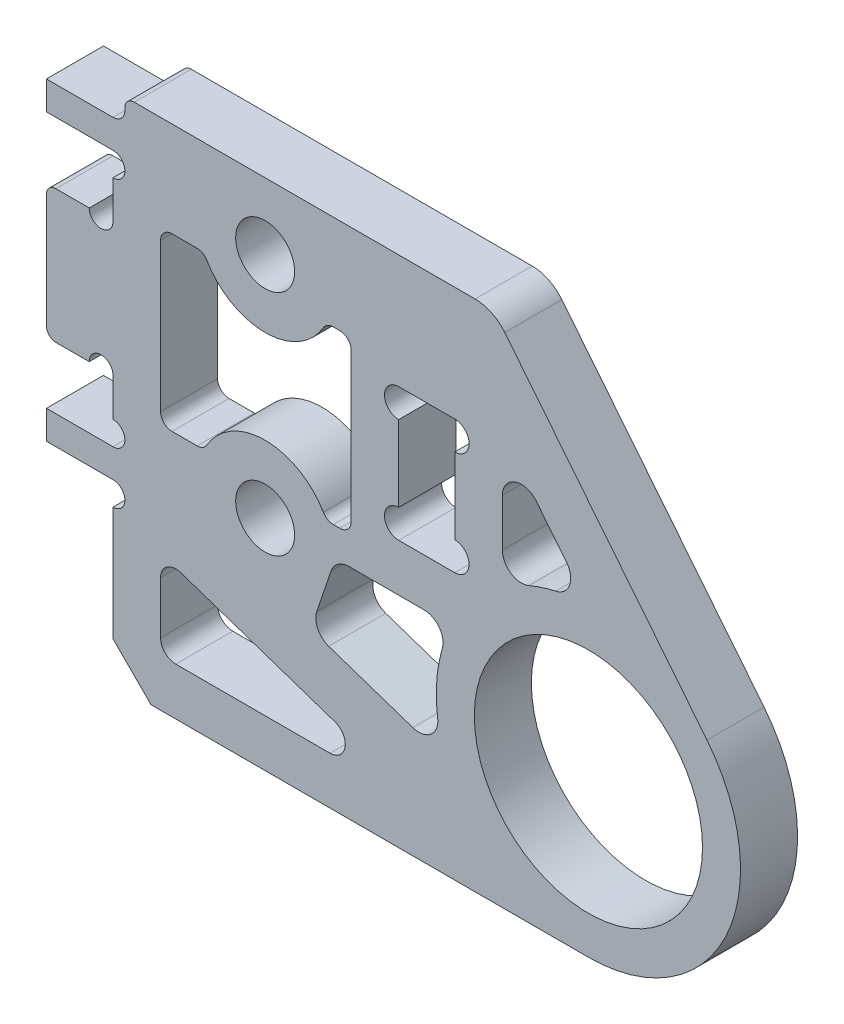
SolidWorks part; units mm, degrees
ref_plane "前视基准面" through (0, 0, 0) normal (0, 0, 1) x (1, 0, 0)
ref_plane "上视基准面" through (0, 0, 0) normal (0, 1, 0) x (1, 0, 0)
ref_plane "右视基准面" through (0, 0, 0) normal (1, 0, 0) x (0, 0, -1)
sketch "草图1" plane through (0, 0, 0) normal (0, 0, 1) x (1, 0, 0)
  line L0 (-5, 19) -> (6.2372, 5.0098)
  line L1 (-25, 19) -> (-25, 0)
  line L3 (-25, 19) -> (-5, 19)
  line L4 (-25, 0) -> (-2.56, -7.5793)
  arc A0 (-2.56, -7.5793) -> (6.2372, 5.0098) centre (0, 0) ccw
  circle A1 centre (0, 0) radius 6
  point P4 (-25, 9.5)
  dimension "D1" = 16
  dimension "D2" = 12
  dimension "D3" = 9.5
  dimension "D4" = 19
  dimension "D5" = 25
  dimension "D6" = 20
extrude "凸台-拉伸1" add sketch "草图1" along normal mid plane 3
sketch "草图2" plane through (0, 0, 1.5) normal (0, 0, 1) x (1, 0, 0)
  line L0 (-25, 19) -> (-25, 0) construction
  line L1 (-25, 13) -> (-28.5, 13)
  line L2 (-25, 13) -> (-25, 6)
  line L3 (-25, 6) -> (-28.5, 6)
  line L4 (-28.5, 13) -> (-28.5, 6)
  line L5 (-28.5, 9.5) -> (-25, 9.5) construction
  line L6 (-28.5, 1.25) -> (-25, 1.25)
  line L7 (-28.5, 16.25) -> (-25, 16.25)
  line L8 (-28.5, 16.25) -> (-28.5, 17.75)
  line L9 (-28.5, 17.75) -> (-25, 17.75)
  line L10 (-25, 16.25) -> (-25, 17.75)
  line L11 (-28.5, 16.25) -> (-25, 17.75) construction
  line L12 (-28.5, 17.75) -> (-25, 16.25) construction
  line L13 (-25, 2.75) -> (-25, 1.25)
  line L14 (-28.5, 2.75) -> (-25, 2.75)
  line L15 (-28.5, 2.75) -> (-28.5, 1.25)
  point P6 (-25, 9.5)
  point P9 (-26.75, 17)
  dimension "D1" = 7
  dimension "D2" = 3.5
  dimension "D3" = 15
  dimension "D4" = 1.5
extrude "凸台-拉伸2" add sketch "草图2" against normal blind 3
sketch "草图3" plane through (0, 0, 1.5) normal (0, 0, 1) x (1, 0, 0)
  line L0 (-25, 16.25) -> (-25, 13) construction
  line L1 (-25, 19) -> (-25, 17.75) construction
  line L2 (-25, 6) -> (-25, 2.75) construction
  line L4 (-25, 1.25) -> (-25, 0) construction
  line L5 (-28.5, 6) -> (-25, 6) construction
  line L6 (-25, 13) -> (-28.5, 13) construction
  circle A0 centre (-25, 15.625) radius 0.625
  circle A1 centre (-25, 18.375) radius 0.625
  circle A2 centre (-25, 3.375) radius 0.625
  circle A3 centre (-25, 0.625) radius 0.625
  circle A6 centre (-25.625, 6) radius 0.625
  circle A7 centre (-25.625, 13) radius 0.625
extrude "切除-拉伸1" cut sketch "草图3" against normal through all
fillet "圆角1" radius 0.5 3 edges at (-25, 19, 0) (-28.5, 6, 0) (-28.5, 13, 0)
sketch "草图4" plane through (0, 0, -1.5) normal (0, 0, -1) x (-1, 0, 0)
  line L0 (26.25, 13) -> (28, 13) construction
  line L1 (7.025, 6) -> (9.975, 6)
  line L2 (7.025, 6) -> (7.025, 13)
  line L3 (7.025, 13) -> (9.975, 13)
  line L4 (9.975, 6) -> (9.975, 13)
  line L5 (7.025, 6) -> (9.975, 13) construction
  line L6 (7.025, 13) -> (9.975, 6) construction
  line L8 (25, 15) -> (25, 13) construction
  line L9 (17, 15.5) -> (17, 3.5) construction
  circle A0 centre (17, 15.5) radius 1.55
  circle A1 centre (17, 3.5) radius 1.55
  point P0 (8.5, 9.5)
  point P13 (17, 9.5)
  dimension "D4" = 3.1
  dimension "D1" = 7
  dimension "D2" = 2.95
  dimension "D3" = 16.5
  dimension "D5" = 12
  dimension "D6" = 8
extrude "切除-拉伸2" cut sketch "草图4" against normal through all
sketch "草图5" plane through (0, 0, -1.5) normal (0, 0, -1) x (-1, 0, 0)
  line L0 (7.025, 13) -> (7.025, 6) construction
  line L1 (9.975, 6) -> (9.975, 13) construction
  circle A0 centre (7.025, 12.25) radius 0.75
  circle A1 centre (9.975, 12.25) radius 0.75
  circle A2 centre (7.025, 6.75) radius 0.75
  circle A3 centre (9.975, 6.75) radius 0.75
  dimension "D1" = 1.5
extrude "切除-拉伸3" cut sketch "草图5" against normal through all
sketch "草图6" plane through (0, 0, -1.5) normal (0, 0, -1) x (-1, 0, 0)
  line L0 (12.475, 14) -> (12.475, 5)
  line L1 (12.475, 5) -> (13.7825, 5)
  line L2 (20.2175, 5) -> (22.5, 5)
  line L3 (22.5, 5) -> (22.5, 14)
  line L4 (22.5, 14) -> (20.2175, 14)
  line L5 (12.475, 14) -> (13.7825, 14)
  line L6 (9.975, 7.5) -> (9.975, 11.5) construction
  line L7 (25, 15) -> (25, 13) construction
  line L8 (5, 19) -> (23.882, 19) construction
  arc A0 (13.7825, 14) -> (20.2175, 14) centre (17, 15.5) ccw
  arc A1 (20.2175, 5) -> (13.7825, 5) centre (17, 3.5) ccw
  circle A2 centre (17, 15.5) radius 1.55 construction
  point P21 (25, 14)
  dimension "D1" = 2
  dimension "D2" = 2.5
  dimension "D3" = 2.5
  dimension "D4" = 5
extrude "切除-拉伸4" cut sketch "草图6" against normal through all
fillet "圆角2" radius 0.6 8 edges at (-13.7825, 14, 0) (-20.2175, 14, 0) (-22.5, 14, 0) (-22.5, 5, 0) (-20.2175, 5, 0) (-13.7825, 5, 0) (-12.475, 5, 0) (-12.475, 14, 0)
sketch "草图7" plane through (0, 0, -1.5) normal (0, 0, -1) x (-1, 0, 0)
  line L0 (7.1937, 3.5) -> (13.3057, 3.5)
  line L1 (13.3057, 3.5) -> (14.6043, -0.3447)
  line L2 (14.6043, -0.3447) -> (7.5166, -2.7387)
  line L3 (25, 0) -> (2.56, -7.5793) construction
  line L4 (4.525, 13.618) -> (0.0125, 8)
  line L6 (4.525, 13.618) -> (4.525, 6.5973)
  line L7 (7.025, 11.5) -> (7.025, 7.5) construction
  line L8 (-6.2372, 5.0098) -> (5, 19) construction
  line L9 (7.025, 6) -> (9.975, 6) construction
  arc A0 (7.5166, -2.7387) -> (7.1937, 3.5) centre (0, 0) ccw
  circle A1 centre (17, 3.5) radius 1.55 construction
  arc A2 (4.525, 6.5973) -> (0.0125, 8) centre (0, 0) ccw
  dimension "D1" = 3
  dimension "D2" = 2.5
  dimension "D3" = 3.5
  dimension "D4" = 2.5
  dimension "D5" = 3
extrude "切除-拉伸5" cut sketch "草图7" against normal through all
fillet "圆角3" radius 1 7 edges at (-0.0125, 8, 0) (-4.525, 13.618, 0) (-4.525, 6.5973, 0) (-13.3057, 3.5, 0) (-14.6043, -0.3447, 0) (-7.5166, -2.7387, 0) (-7.1937, 3.5, 0)
sketch "草图8" plane through (0, 0, 1.5) normal (0, 0, 1) x (1, 0, 0)
  line L0 (-25, 0) -> (-25, -8)
  line L1 (-25, -8) -> (0, -8)
  line L2 (-25, 0) -> (-2.56, -7.5793) construction
  line L3 (-25, 0) -> (-22.5, -0.8444)
  line L4 (-22.5, -0.8444) -> (-22.5, -5.5)
  line L5 (-22.5, -5.5) -> (-8.7163, -5.5)
  line L6 (-8.7163, -5.5) -> (-2.56, -7.5793)
  arc A0 (-2.56, -7.5793) -> (6.2372, 5.0098) centre (0, 0) ccw construction
  arc A1 (-2.56, -7.5793) -> (0, -8) centre (0, 0) ccw
  dimension "D1" = 2.5
  dimension "D2" = 2.5
extrude "凸台-拉伸3" add sketch "草图8" against normal blind 3
fillet "圆角4" radius 0.8 3 edges at (-8.7163, -5.5, 0) (-22.5, -5.5, 0) (-22.5, -0.8444, 0)
chamfer "倒角1" distance 2 angle 45 1 edges at (-25, -8, 0)
fillet "圆角6" radius 2 1 edges at (-5, 19, 0)
